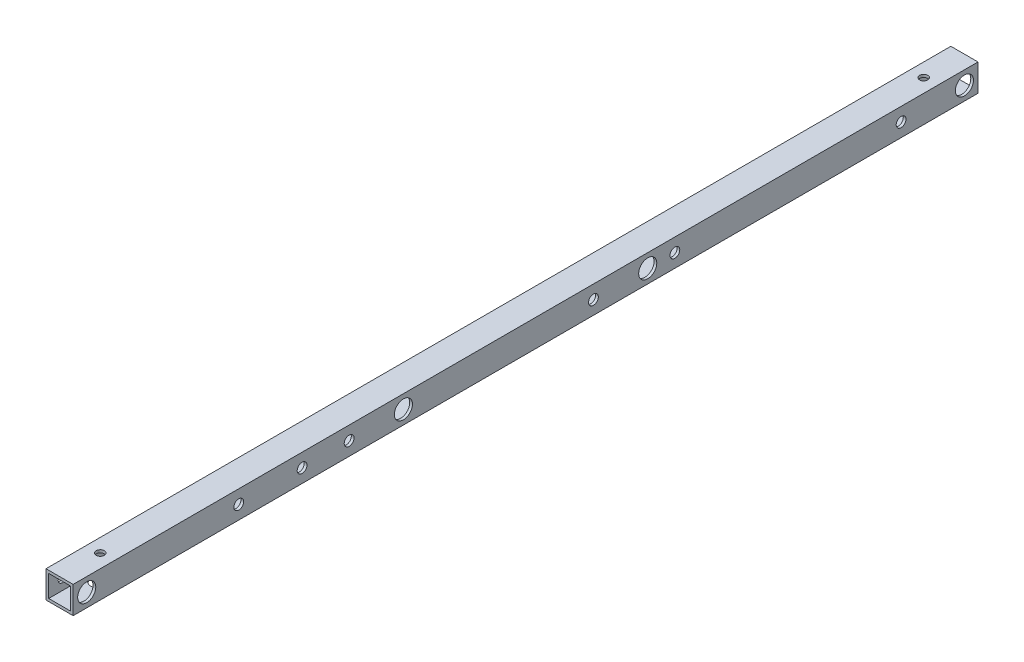
SolidWorks part; units mm, degrees
material "6063-T5"
ref_plane "正面" through (0, 0, 0) normal (0, 0, 1) x (1, 0, 0)
ref_plane "平面" through (0, 0, 0) normal (0, 1, 0) x (1, 0, 0)
ref_plane "右側面" through (0, 0, 0) normal (1, 0, 0) x (0, 0, -1)
sketch "ｽｹｯﾁ1" plane through (0, 0, 0) normal (0, 0, 1) x (1, 0, 0)
  line L1 (-7.5, -7.5) -> (7.5, -7.5)
  line L2 (-7.5, -7.5) -> (-7.5, 7.5)
  line L3 (-7.5, 7.5) -> (7.5, 7.5)
  line L4 (7.5, -7.5) -> (7.5, 7.5)
  line L5 (-7.5, -7.5) -> (7.5, 7.5) construction
  line L6 (-7.5, 7.5) -> (7.5, -7.5) construction
  line L7 (-6, -6) -> (6, -6)
  line L8 (-6, -6) -> (-6, 6)
  line L9 (-6, 6) -> (6, 6)
  line L10 (6, -6) -> (6, 6)
  line L11 (-6, -6) -> (6, 6) construction
  line L12 (-6, 6) -> (6, -6) construction
  point P0 (0, 0)
  point P6 (0, 0)
  dimension "D1" = 1.5
  dimension "D2" = 15
  dimension "D3" = 15
extrude "ﾎﾞｽ - 押し出し1" add sketch "ｽｹｯﾁ1" along normal blind 500
sketch "ｽｹｯﾁ2" plane through (7.5, 0, 0) normal (1, 0, 0) x (0, 0, -1)
  line L0 (-500, -7.5) -> (0, -7.5) construction
  line L1 (0, -7.5) -> (0, 7.5) construction
  line L2 (-500, -7.5) -> (-500, 7.5) construction
  line L3 (-500, 7.5) -> (0, 7.5) construction
  circle A4 centre (-492.5, 0) radius 2.25
  circle A8 centre (-7.5, 0) radius 2.25
  circle A9 centre (-317.5, 0) radius 2.25
  circle A10 centre (-182.5, 0) radius 2.25
  point P16 (-250, 7.5)
  dimension "D1" = 4.5
  dimension "D2" = 7.5
  dimension "D3" = 7.5
  dimension "D6" = 67.5
  dimension "D7" = 2
  dimension "D8" = 135
  dimension "D4" = 7.5
  dimension "D9" = 2
  dimension "D5" = 2
extrude "ｶｯﾄ - 押し出し1" cut sketch "ｽｹｯﾁ2" against normal blind 25
sketch "ｽｹｯﾁ4" plane through (0, -7.5, 0) normal (0, -1, 0) x (-1, 0, 0)
  line L2 (7.5, 0) -> (-7.5, 0) construction
  line L3 (-7.5, -500) -> (-7.5, 0) construction
  line L4 (7.5, -500) -> (-7.5, -500) construction
  line L5 (7.5, -500) -> (7.5, 0) construction
  circle A2 centre (0, -22.5) radius 2.25
  circle A3 centre (0, -477.5) radius 2.25
  dimension "D1" = 22.5
  dimension "D2" = 7.5
  dimension "D3" = 4.5
  dimension "D6" = 4.5
  dimension "D8" = 22.5
  dimension "D4" = 7.5
extrude "ｶｯﾄ - 押し出し3" cut sketch "ｽｹｯﾁ4" against normal blind 20
sketch "ｽｹｯﾁ5" plane through (7.5, 0, 0) normal (1, 0, 0) x (0, 0, -1)
  circle A0 centre (-492.5, 0) radius 5
  circle A1 centre (-7.5, 0) radius 5
  circle A2 centre (-182.5, 0) radius 5
  circle A3 centre (-317.5, 0) radius 5
  dimension "D1" = 10
  dimension "D2" = 10
  dimension "D3" = 10
  dimension "D4" = 10
extrude "ｶｯﾄ - 押し出し4" cut sketch "ｽｹｯﾁ5" against normal blind 3.3
sketch "ｽｹｯﾁ6" plane through (0, -7.5, 0) normal (0, 1, 0) x (1, 0, 0)
  circle A0 centre (0, -22.5) radius 5
  circle A2 centre (0, -477.5) radius 5
  dimension "D2" = 10
  dimension "D3" = 10
extrude "ｶｯﾄ - 押し出し5" cut sketch "ｽｹｯﾁ6" along normal blind 3.3
sketch "ｽｹｯﾁ7" plane through (7.5, 0, 0) normal (1, 0, 0) x (0, 0, -1)
  line L0 (-500, -7.5) -> (-500, 7.5) construction
  circle A0 centre (-317.5, 0) radius 5 construction
  circle A1 centre (-182.5, 0) radius 5 construction
  point P0 (-347.5, 0)
  point P1 (-212.5, 0)
  point P6 (-500, 0)
  point P8 (-167.5, 0)
  point P10 (-42.5, 0)
  point P15 (-373.5, 0)
  point P17 (-408.5, 0)
  dimension "D2" = 30
  dimension "D4" = 15
  dimension "D1" = 135
  dimension "D3" = 125
  dimension "D5" = 35
  dimension "D6" = 26
hole_wizard "Ø5.4 (5.4) 直径の穴1" positions "ｽｹｯﾁ7" profile "ｽｹｯﾁ8" hole size "Ø5.4" standard "JIS" end condition through all
sketch "ｽｹｯﾁ8" plane through (7.5, 0, 347.5) normal (0, 1, 0) x (0, 0, -1)
  line L0 (0, 0) -> (0, 15)
  line L1 (0, 15) -> (2.7, 15)
  line L2 (2.7, 15) -> (2.7, 0)
  line L5 (2.7, 0) -> (0, 0)
  line L11 (0, -6.35) -> (0, 107.95) construction
  dimension "通し穴の直径" = 5.4
  dimension "通し穴の深さ" = 15
hole_wizard "Ø10.0 (10) 直径の穴1" positions "ｽｹｯﾁ9" profile "ｽｹｯﾁ11" hole size "Ø10.0" standard "JIS"
sketch "ｽｹｯﾁ9" plane through (-7.5, 0, 0) normal (-1, 0, 0) x (0, 0, 1)
  point P0 (347.5, 0)
  point P3 (212.5, 0)
  point P6 (167.5, 0)
  point P9 (42.5, 0)
  point P13 (373.5, 0)
  point P16 (408.5, 0)
sketch "ｽｹｯﾁ11" plane through (-7.5, 0, 347.5) normal (0, 1, 0) x (0, 0, 1)
  line L0 (0, 0) -> (0, 4.5043)
  line L1 (0, 4.5043) -> (5, 1.5)
  line L2 (5, 1.5) -> (5, 0)
  line L5 (5, 0) -> (0, 0)
  line L10 (0, 4.5043) -> (-5, 1.5) construction
  line L11 (0, -6.35) -> (0, 107.95) construction
  dimension "穴の直径" = 10
  dimension "穴の深さ" = 1.5
  dimension "ﾄﾞﾘﾙ角度" = 118
